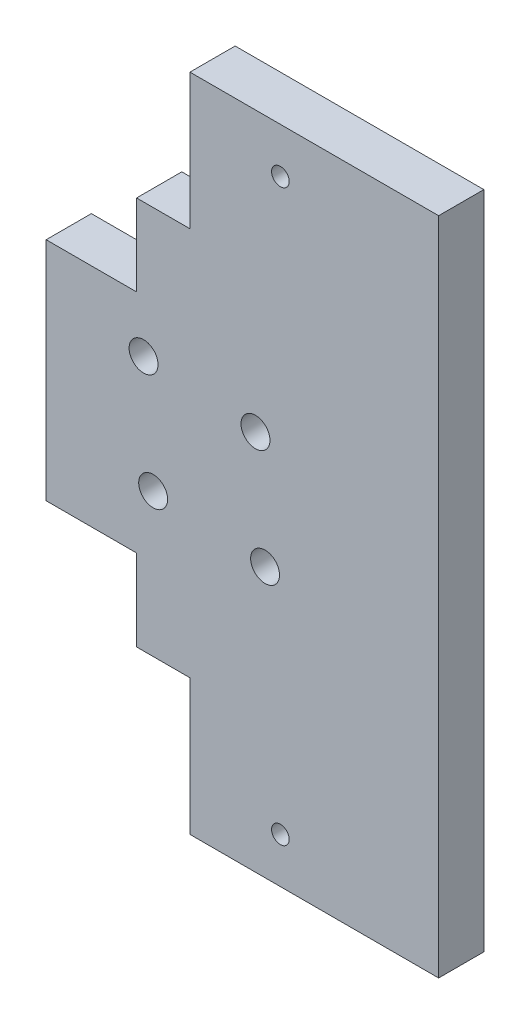
SolidWorks part; units mm, degrees
ref_plane "Front Plane" through (0, 0, 0) normal (0, 0, 1) x (1, 0, 0)
ref_plane "Top Plane" through (0, 0, 0) normal (0, 1, 0) x (1, 0, 0)
ref_plane "Right Plane" through (0, 0, 0) normal (1, 0, 0) x (0, 0, -1)
sketch "Sketch1" plane through (0, 0, 0) normal (0, 0, 1) x (1, 0, 0)
  line L1 (-19.2, 36.5) -> (19.2, 36.5)
  line L2 (-19.2, 36.5) -> (-19.2, -36.5)
  line L3 (-19.2, -36.5) -> (19.2, -36.5)
  line L4 (19.2, 36.5) -> (19.2, -36.5)
  line L5 (-19.2, 36.5) -> (19.2, -36.5) construction
  line L6 (-19.2, -36.5) -> (19.2, 36.5) construction
  point P0 (0, 0)
  dimension "D1" = 73
  dimension "D2" = 38.4
extrude "Boss-Extrude1" add sketch "Sketch1" along normal blind 5
sketch "Sketch4" plane through (-19.2, 0, 0) normal (-1, 0, 0) x (0, 0, 1)
  line L0 (5, 0) -> (0, 0) construction
  line L1 (5, 36.5) -> (5, -36.5) construction
  line L2 (0, 36.5) -> (0, -36.5) construction
  line L4 (0, -12.5) -> (5, -12.5)
  line L5 (0, -12.5) -> (0, 12.5)
  line L6 (0, 12.5) -> (5, 12.5)
  line L7 (5, -12.5) -> (5, 12.5)
  line L8 (0, -12.5) -> (5, 12.5) construction
  line L9 (0, 12.5) -> (5, -12.5) construction
  point P6 (2.5, 0)
  dimension "D1" = 25
extrude "Boss-Extrude3" add sketch "Sketch4" along normal blind 10
sketch "Sketch5" plane through (0, 0, 5) normal (0, 0, 1) x (1, 0, 0)
  line L0 (-19.2, -12.5) -> (-19.2, 12.5) construction
  line L1 (-19.2, 0) -> (-11.71, 0) construction
  line L2 (-11.71, 0) -> (-18.4275, 6.7175) construction
  line L3 (-11.71, 0) -> (-6.0531, 5.6569) construction
  line L4 (-11.71, 0) -> (-4.9925, -6.7175) construction
  line L5 (-11.71, 0) -> (-17.3669, -5.6569) construction
  circle A0 centre (-18.4275, 6.7175) radius 1.6
  circle A1 centre (-6.0531, 5.6569) radius 1.6
  circle A2 centre (-17.3669, -5.6569) radius 1.6
  circle A3 centre (-4.9925, -6.7175) radius 1.6
  dimension "D1" = 7.49
extrude "Cut-Extrude1" cut sketch "Sketch5" against normal blind 25
sketch "Sketch6" plane through (-19.2, 0, 0) normal (-1, 0, 0) x (0, 0, 1)
  line L0 (0, -12.5) -> (0, -36.5) construction
  line L1 (5, -36.5) -> (0, -36.5)
  line L2 (5, -36.5) -> (5, -21.5)
  line L3 (5, -21.5) -> (0, -21.5)
  line L4 (0, -36.5) -> (0, -21.5)
  line L5 (0, -12.5) -> (0, 12.5) construction
  line L6 (0, 0) -> (22.9115, 0) construction
  line L7 (5, 21.5) -> (0, 21.5)
  line L8 (0, 36.5) -> (0, 21.5)
  line L9 (5, 36.5) -> (0, 36.5)
  line L10 (5, 36.5) -> (5, 21.5)
  dimension "D1" = 15
extrude "Cut-Extrude2" cut sketch "Sketch6" against normal blind 5.9 contours L10 L9 L8 L7 | L2 L1 L4 L3
sketch "Sketch8" plane through (0, 0, 0) normal (0, 0, -1) x (-1, 0, 0)
  line L0 (13.3, -36.5) -> (-19.2, -36.5) construction
  line L1 (-19.2, 36.5) -> (-14.2, 36.5)
  line L2 (-19.2, 36.5) -> (-19.2, -36.5)
  line L3 (-19.2, -36.5) -> (-14.2, -36.5)
  line L4 (-14.2, 36.5) -> (-14.2, -36.5)
  dimension "D1" = 5
extrude "Cut-Extrude3" cut sketch "Sketch8" against normal blind 10
sketch "Sketch9" plane through (0, 0, 0) normal (0, 0, -1) x (-1, 0, 0)
  line L0 (13.3, 36.5) -> (13.3, 31.5) construction
  line L1 (13.3, 36.5) -> (13.3, 21.5) construction
  line L2 (13.3, 31.5) -> (3.3, 31.5) construction
  line L3 (13.3, -36.5) -> (13.3, -31.5) construction
  line L4 (13.3, -36.5) -> (13.3, -21.5) construction
  line L5 (13.3, -36.5) -> (-14.2, -36.5) construction
  line L6 (13.3, -31.5) -> (3.3, -31.5) construction
  circle A0 centre (3.3, 31.5) radius 0.975
  circle A1 centre (3.3, -31.5) radius 0.975
extrude "Cut-Extrude4" cut sketch "Sketch9" against normal blind 13
